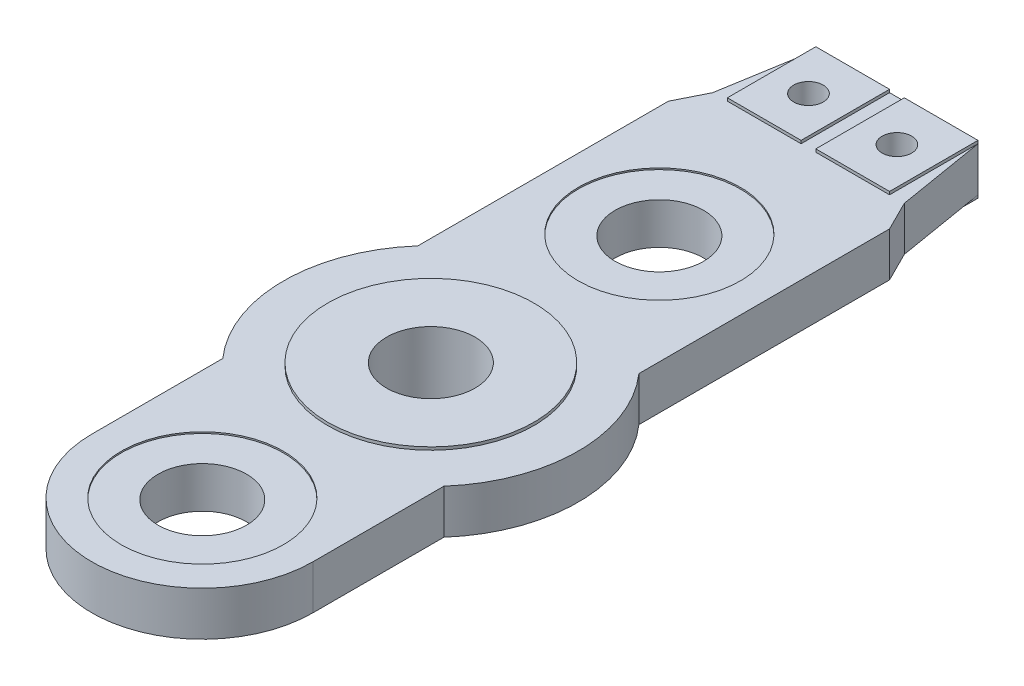
SolidWorks part; units mm, degrees
ref_plane "Front Plane" through (0, 0, 0) normal (0, 0, 1) x (1, 0, 0)
ref_plane "Top Plane" through (0, 0, 0) normal (0, 1, 0) x (1, 0, 0)
ref_plane "Right Plane" through (0, 0, 0) normal (1, 0, 0) x (0, 0, -1)
sketch "Sketch1" plane through (0, 0, 0) normal (0, 1, 0) x (1, 0, 0)
  line L0 (0, 7.75) -> (0, -7.75) construction
  line L1 (-3.75, -7.75) -> (-3.75, -3.3072)
  line L2 (3.75, -7.75) -> (3.75, -3.3072)
  line L3 (3.75, 3.3072) -> (3.75, 11.8072)
  line L4 (-3.75, 3.3072) -> (-3.75, 11.8072)
  line L5 (-3.75, 11.8072) -> (-3.25, 12.8072)
  line L6 (-3.25, 12.8072) -> (-2.75, 15.8072)
  line L7 (-2.75, 15.8072) -> (2.75, 15.8072)
  line L8 (2.75, 15.8072) -> (3.25, 12.8072)
  line L9 (3.25, 12.8072) -> (3.75, 11.8072)
  line L10 (-1.5, 14.3072) -> (1.5, 14.3072) construction
  arc A0 (-3.75, 3.3072) -> (-3.75, -3.3072) centre (0, 0) ccw
  circle A1 centre (0, -7.75) radius 1.5
  arc A2 (-3.75, -7.75) -> (3.75, -7.75) centre (0, -7.75) ccw
  circle A3 centre (0, 7.75) radius 1.5
  circle A4 centre (0, 7.75) radius 3.75 construction
  arc A5 (-2.0044, 4.5806) -> (-3.75, 3.3072) centre (0, 0) ccw construction
  arc A6 (0, 5) -> (-2.0044, 4.5806) centre (0, 0) ccw construction
  arc A7 (3.75, 3.3072) -> (2.0044, 4.5806) centre (0, 0) ccw construction
  arc A8 (2.0044, 4.5806) -> (0, 5) centre (0, 0) ccw construction
  arc A9 (2.0044, -4.5806) -> (3.75, -3.3072) centre (0, 0) ccw construction
  arc A10 (3.75, -3.3072) -> (3.75, 3.3072) centre (0, 0) ccw
  arc A11 (2.0044, -4.5806) -> (0, -4) centre (0, -7.75) ccw construction
  arc A12 (0, -5) -> (2.0044, -4.5806) centre (0, 0) ccw construction
  arc A13 (3.75, -7.75) -> (2.0044, -4.5806) centre (0, -7.75) ccw construction
  arc A14 (0, -4) -> (-2.0044, -4.5806) centre (0, -7.75) ccw construction
  arc A15 (-2.0044, -4.5806) -> (0, -5) centre (0, 0) ccw construction
  arc A16 (-2.0044, -4.5806) -> (-3.75, -7.75) centre (0, -7.75) ccw construction
  arc A17 (-3.75, -3.3072) -> (-2.0044, -4.5806) centre (0, 0) ccw construction
  circle A18 centre (-1.5, 14.3072) radius 0.5
  circle A19 centre (1.5, 14.3072) radius 0.5
  circle A20 centre (0, 0) radius 1.5
  point P10 (0, 0)
  point P24 (0, 15.8072)
  point P33 (0, 14.3072)
  point P34 (-3, 14.3072)
  dimension "D1" = 3
  dimension "D2" = 7.5
  dimension "D4" = 10
  dimension "D12" = 1
  dimension "D13" = 3
  dimension "D3" = 15.5
  dimension "D5" = 8.5
  dimension "D6" = 0.5
  dimension "D7" = 1
  dimension "D8" = 0.5
  dimension "D9" = 4
  dimension "D10" = 1
  dimension "D11" = 3
extrude "Boss-Extrude1" add sketch "Sketch1" along normal blind 1.5
sketch "Sketch2" plane through (0, 1.5, 0) normal (0, 1, 0) x (1, 0, 0)
  circle A0 centre (0, 0) radius 3.5
  arc A1 (3.75, -3.3072) -> (3.75, 3.3072) centre (0, 0) ccw construction
  circle A2 centre (0, 0) radius 1.5 construction
  circle A3 centre (0, 0) radius 1.5
  dimension "D1" = 1.5
extrude "Boss-Extrude2" add sketch "Sketch2" along normal blind 0.1
sketch "Sketch3" plane through (0, 1.5, 0) normal (0, 1, 0) x (1, 0, 0)
  circle A2 centre (0, -7.75) radius 2.75
  circle A3 centre (0, -7.75) radius 2.75
  circle A7 centre (0, 7.75) radius 2.75
  circle A8 centre (0, 7.75) radius 2.75
  dimension "D1" = 1.25
  dimension "D2" = 1.25
extrude "Cut-Extrude1" cut sketch "Sketch3" against normal blind 0.05
sketch "Sketch4" plane through (0, 0, 0) normal (0, -1, 0) x (1, 0, 0)
  circle A0 centre (0, -7.75) radius 2.75 construction
  circle A1 centre (0, 7.75) radius 2.75 construction
  circle A2 centre (0, -7.75) radius 2.75
  circle A3 centre (0, 7.75) radius 2.75
extrude "Cut-Extrude2" cut sketch "Sketch4" against normal blind 0.05
sketch "Sketch5" plane through (0, 0, 0) normal (0, -1, 0) x (1, 0, 0)
  circle A0 centre (0, 0) radius 2.75
  circle A1 centre (0, 0) radius 1.5 construction
  circle A2 centre (0, 0) radius 1.5
  dimension "D1" = 5.5
extrude "Boss-Extrude3" add sketch "Sketch5" along normal blind 1.5
fillet "Fillet1" radius 0.5 1 edges at (0, 0, 2.75)
sketch "Sketch6" plane through (0, 1.5, 0) normal (0, 1, 0) x (1, 0, 0)
  line L1 (-2.75, 15.8072) -> (-0.25, 15.8072)
  line L2 (-2.75, 15.8072) -> (-2.75, 12.8072)
  line L3 (-2.75, 12.8072) -> (-0.25, 12.8072)
  line L4 (-0.25, 15.8072) -> (-0.25, 12.8072)
  line L5 (-2.75, 15.8072) -> (-0.25, 12.8072) construction
  line L6 (-2.75, 12.8072) -> (-0.25, 15.8072) construction
  line L7 (2.75, 15.8072) -> (0.25, 15.8072)
  line L8 (2.75, 15.8072) -> (2.75, 12.8072)
  line L9 (2.75, 12.8072) -> (0.25, 12.8072)
  line L10 (0.25, 15.8072) -> (0.25, 12.8072)
  line L11 (2.75, 15.8072) -> (0.25, 12.8072) construction
  line L12 (2.75, 12.8072) -> (0.25, 15.8072) construction
  circle A0 centre (1.5, 14.3072) radius 0.5 construction
  circle A1 centre (-1.5, 14.3072) radius 0.5 construction
  circle A2 centre (1.5, 14.3072) radius 0.5
  circle A3 centre (-1.5, 14.3072) radius 0.5
  point P10 (-1.5, 14.3072)
  point P16 (1.5, 14.3072)
  point P18 (0, 0)
  point P19 (0, 0)
extrude "Boss-Extrude4" add sketch "Sketch6" along normal blind 0.1
sketch "Sketch7" plane through (0, 0, 0) normal (0, -1, 0) x (1, 0, 0)
  line L0 (-2.75, -15.8072) -> (-2.75, -12.8072) construction
  line L1 (-2.75, -12.8072) -> (-0.25, -12.8072) construction
  line L2 (-0.25, -12.8072) -> (-0.25, -15.8072) construction
  line L3 (-0.25, -15.8072) -> (-2.75, -15.8072) construction
  line L4 (2.75, -12.8072) -> (2.75, -15.8072) construction
  line L5 (2.75, -15.8072) -> (0.25, -15.8072) construction
  line L6 (0.25, -15.8072) -> (0.25, -12.8072) construction
  line L7 (0.25, -12.8072) -> (2.75, -12.8072) construction
  line L8 (-2.75, -15.8072) -> (-2.75, -12.8072)
  line L9 (-2.75, -12.8072) -> (-0.25, -12.8072)
  line L10 (-0.25, -12.8072) -> (-0.25, -15.8072)
  line L11 (-0.25, -15.8072) -> (-2.75, -15.8072)
  line L12 (2.75, -12.8072) -> (2.75, -15.8072)
  line L13 (2.75, -15.8072) -> (0.25, -15.8072)
  line L14 (0.25, -15.8072) -> (0.25, -12.8072)
  line L15 (0.25, -12.8072) -> (2.75, -12.8072)
  circle A0 centre (-1.5, -14.3072) radius 0.5 construction
  circle A1 centre (1.5, -14.3072) radius 0.5 construction
  circle A2 centre (-1.5, -14.3072) radius 0.5
  circle A3 centre (1.5, -14.3072) radius 0.5
extrude "Boss-Extrude5" add sketch "Sketch7" along normal blind 0.1
